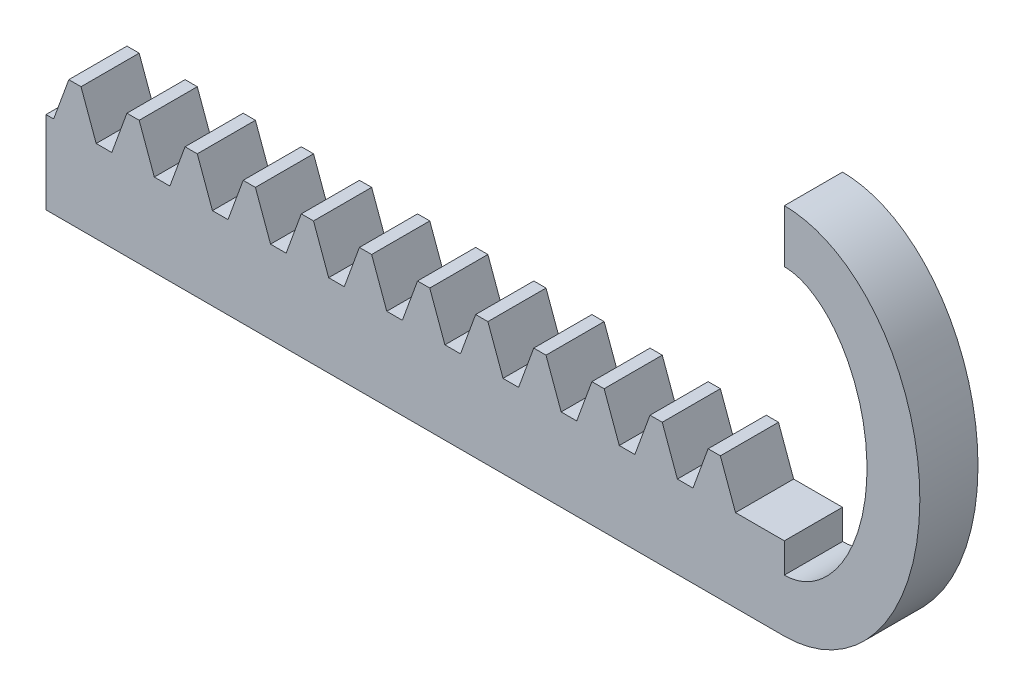
SolidWorks part; units mm, degrees
extrude "Blank" add sketch "BlankSke" against normal blind 10
sketch "BlankSke" plane through (0, 0, 0) normal (0, 0, 1) x (1, 0, 0)
  line L1 (0, 0) -> (100, 0)
  line L2 (0, 0) -> (0, 11.75)
  line L3 (0, 11.75) -> (100, 11.75)
  line L4 (100, 0) -> (100, 11.75)
  dimension "Length" = 100
  dimension "Blank_height" = 11.75
ref_plane "Plane1" through (0, 0, 0) normal (0, 0, 1) x (1, 0, 0)
ref_plane "Plane2" through (0, 0, 0) normal (0, 1, 0) x (1, 0, 0)
ref_plane "Plane3" through (0, 0, 0) normal (1, 0, 0) x (0, 0, -1)
other "Configuration Table"
sketch "HoldingSke" plane through (0, 0, 0) normal (0, 1, 0) x (1, 0, 0)
  line L0 (0, 0) -> (0.0795, 0.5659)
  line L1 (-15, 0) -> (100, 0) construction
  line L2 (0, 0) -> (-2.1039, 2.3779)
  line L3 (0, 0) -> (-11.863, 4.5341)
  line L4 (0, 0) -> (8.1152, 2.9537)
  line L5 (0, 0) -> (-23.7986, -8.8762)
  line L6 (0, 0) -> (-10.5278, -7.1032)
  line L9 (-71.009, 38.7566) -> (22.9603, 72.9586)
  line L10 (-76.2, 4.1279) -> (-66.2, 4.1279)
  line L11 (0, 0) -> (-10, 0)
  line L12 (-76.2, 101.6) -> (-76.147, 101.6)
  line L13 (24.9733, 27.94) -> (52.9518, 28.4284)
  line L14 (24.9733, 27.94) -> (24.9743, 27.94)
  line L15 (24.9733, 27.94) -> (100.4006, 29.5858)
  circle A0 centre (0, 0) radius 19.05
  circle A1 centre (0, 0) radius 5
  circle A2 centre (0, 0) radius 12.7
  dimension "MPH" = 10
  dimension "Diameter" = 38.1
  dimension "Num_teeth" = 20
  dimension "Pitch" = 0.5714
  dimension "Show_teeth" = 998
  dimension "Thickness" = 12.7
  dimension "Ap" = 20
  dimension "Pitch_height" = 10
  dimension "Width" = 10
  dimension "Backlash" = 0.053
  dimension "Addendum_fac" = 1
  dimension "Dedendum_fac" = 1.25
  dimension "Clearance_fac" = 0.25
  dimension "Dedendum_add" = 0.001
  dimension "Length" = 100
  dimension "Module" = 1.75
sketch "TooCutSkeIll" plane through (0, 0, 0) normal (0, 0, 1) x (1, 0, 0)
  line L0 (-2.1536, 11.7039) -> (-0.8423, 8.101)
  line L1 (-0.4302, 7.8125) -> (0.4302, 7.8125)
  line L2 (0.8423, 8.101) -> (2.1536, 11.7039)
  line L3 (100, 11.75) -> (0, 11.75) construction
  line L4 (0, 0) -> (0, 64.897) construction
  line L5 (-13.208, 10) -> (12.954, 10) construction
  line L6 (0, 0) -> (100, 0) construction
  line L7 (1.5334, 10) -> (1.5334, 48.7463) construction
  line L8 (-1.5334, 10) -> (-1.5334, 48.7463) construction
  line L9 (2.2194, 11.75) -> (2.2194, 11.7754)
  line L10 (-2.2194, 11.75) -> (-2.2194, 11.7754)
  line L11 (-2.2194, 11.7754) -> (2.2194, 11.7754)
  arc A0 (0.4302, 7.8125) -> (0.8423, 8.101) centre (0.4302, 8.251) ccw
  arc A1 (-0.8423, 8.101) -> (-0.4302, 7.8125) centre (-0.4302, 8.251) ccw
  arc A2 (2.2194, 11.75) -> (2.1536, 11.7039) centre (2.2194, 11.68) ccw
  arc A3 (-2.1536, 11.7039) -> (-2.2194, 11.75) centre (-2.2194, 11.68) ccw
  dimension "Pitch_height" = 10
  dimension "Addendum_plus" = 1.7754
  dimension "Pressure_angle" = 20
  dimension "Gap_width" = 3.0669
  dimension "Dedendum" = 2.1875
extrude "ToothCutIll" [suppressed] cut sketch "TooCutSkeIll" against normal through all
sketch "TooCutSkeSim" plane through (0, 0, 0) normal (0, 0, 1) x (1, 0, 0)
  line L0 (0.7373, 7.8125) -> (-0.7373, 7.8125)
  line L1 (2.1796, 11.7754) -> (0.7373, 7.8125)
  line L2 (0, 17.4625) -> (0, 53.467) construction
  line L3 (2.1796, 11.7754) -> (-2.1796, 11.7754)
  line L6 (-2.1796, 11.7754) -> (-0.7373, 7.8125)
  line L9 (-1.5334, 10) -> (1.5334, 10) construction
  line L10 (0, 0) -> (100, 0) construction
  line L11 (1.5334, 10) -> (1.5334, 53.467) construction
  line L12 (-1.5334, 10) -> (-1.5334, 53.467) construction
  dimension "Pitch_height" = 10
  dimension "Addendum_plus" = 1.7754
  dimension "Pressure_angle" = 20
  dimension "Gap_width" = 3.0669
  dimension "Dedendum" = 2.1875
extrude "ToothCutSim" cut sketch "TooCutSkeSim" against normal through all
pattern_linear "TeethCuts" count 19 spacing 5.4978 along (1, 0, 0) of "ToothCutIll", "ToothCutSim"
sketch "草图3" plane through (0, 0, 0) normal (0, 0, 1) x (1, 0, 0)
  line L0 (100, 0) -> (102.8415, 0)
  line L1 (102.8415, 0) -> (102.8415, 7.8125)
  line L2 (102.8415, 7.8125) -> (100, 7.8125)
  line L3 (100, 7.8125) -> (100, 0)
  line L4 (100, 0) -> (100, 8.6438) construction
  line L5 (98.2229, 7.8125) -> (99.6974, 7.8125) construction
extrude "凸台-拉伸1" add sketch "草图3" against normal up to surface (10 mm away) contours L3 L0 L1 L2 up to face at (50.1593, 9.4613, -10)
sketch "草图5" plane through (0, 0, 0) normal (0, 0, 1) x (1, 0, 0)
  line L0 (102.8415, 0.3026) -> (102.8415, 8.9464) construction
  line L1 (102.8415, 0) -> (102.8415, 5)
  line L2 (102.8415, 35.2664) -> (102.8415, 30.2664)
  arc A0 (102.8415, 0) -> (102.8415, 35.2664) centre (102.8415, 17.6332) ccw construction
  ellipse E0 centre (102.8415, 17.6332) end of major axis (102.8415, 35.2664) minor radius 12.82 (102.8415, 0) -> (102.8415, 35.2664) ccw
  spline S0 degree 1 poles (102.8415, 5) (102.8415, 30.2664) knots 0 0 1 1 construction
  spline S1 degree 3 poles (102.8415, 5) (103.239, 5) (104.0058, 5.1028) (105.6778, 5.7786) (107.9569, 7.7782) (110.1255, 12.1377) (110.9296, 17.6332) (110.1255, 23.1287) (107.9569, 27.4882) (105.6778, 29.4878) (104.0058, 30.1636) (103.239, 30.2664) (102.8415, 30.2664) knots 3.141593 3.141593 3.141593 3.141593 3.337942 3.534292 3.926991 4.31969 4.712389 5.105088 5.497787 5.890486 6.086836 6.283185 6.283185 6.283185 6.283185
  dimension "D1" = 5
extrude "凸台-拉伸2" add sketch "草图5" against normal blind 5.5 contours L2 S1 L1 E0
sketch "草图6" plane through (0, 0, -10) normal (0, 0, -1) x (-1, 0, 0)
  line L1 (-102.8415, 0) -> (0, 0)
  line L2 (-102.8415, 0) -> (-102.8415, 15)
  line L3 (-102.8415, 15) -> (0, 15)
  line L4 (0, 0) -> (0, 15)
  dimension "D1" = 15
extrude "切除-拉伸2" cut sketch "草图6" against normal blind 4.5 contours L2 L1 L4 L3
sketch "草图7" plane through (0, 0, 0) normal (0, 0, 1) x (1, 0, 0)
  line L0 (102.8415, 7.8125) -> (100, 7.8125) construction
  line L1 (99.3518, 9.0173) -> (100.512, 9.0173)
  line L2 (99.3518, 9.0173) -> (99.3518, 7.8125)
  line L3 (99.3518, 7.8125) -> (100.512, 7.8125)
  line L4 (100.512, 9.0173) -> (100.512, 7.8125)
extrude "切除-拉伸3" cut sketch "草图7" against normal up to surface (5.5 mm away) up to face at (53.9987, 9.566, -5.5)
sketch "草图8" plane through (0, 0, 0) normal (-1, 0, 0) x (0, 0, 1)
  line L1 (8.3331, -13.325) -> (-8.3331, -13.325)
  line L2 (8.3331, -13.325) -> (8.3331, 13.325)
  line L3 (8.3331, 13.325) -> (-8.3331, 13.325)
  line L4 (-8.3331, -13.325) -> (-8.3331, 13.325)
  line L5 (8.3331, -13.325) -> (-8.3331, 13.325) construction
  line L6 (8.3331, 13.325) -> (-8.3331, -13.325) construction
  point P0 (0, 0)
extrude "切除-拉伸5" cut sketch "草图8" against normal blind 33
sketch "草图9" plane through (0, 0, 0) normal (0, 0, 1) x (1, 0, 0)
  ellipse E0 centre (102.8415, 17.6332) end of major axis (102.8415, 35.2664) minor radius 12.82 (102.8415, 0) -> (102.8415, 35.2664) ccw construction
  point P0 (115.6438, 16.7056)
sketch "草图10" plane through (0, 0, 0) normal (0, 0, 1) x (1, 0, 0)
  ellipse E0 centre (102.8415, 17.6332) end of major axis (102.8415, 35.2664) minor radius 12.82 (102.8415, 0) -> (102.8415, 35.2664) ccw construction
  point P0 (115.6328, 16.454)
equation "' \"Module@HoldingSke\" = 6.35"
equation "' \"Num_teeth@HoldingSke\" = 12"
equation "' \"Ap@HoldingSke\" =  20"
equation "' \"Ap@HoldingSke\" = 20"
equation "' \"Width@HoldingSke\" = 0.25 * 25.4"
equation "' \"Show_teeth@HoldingSke\" = 500"
equation "' \"Backlash@HoldingSke\" = 0.009 * 25.4"
equation "' \"Addendum_fac@HoldingSke\" = 1.0"
equation "' \"Dedendum_fac@HoldingSke\" = 1.25"
equation "' \"Dedendum_add@HoldingSke\" = 0.00005 * 25.4"
equation "' \"Clearance_fac@HoldingSke\" = 0.25"
equation "' \"Pitch_height@HoldingSke\" = 1 * 25.4"
equation "' \"Length@HoldingSke\" = 4.71 * 25.4"
equation "\"Pitch@HoldingSke\" = 1 / \"Module@HoldingSke\""
equation "\"MPH@HoldingSke\" = \"Dedendum_fac@HoldingSke\" / \"Pitch@HoldingSke\" + 2 * \"Dedendum_add@HoldingSke\" + 0.002 * 25.4"
equation "\"MPH@HoldingSke\" = ((sgn( \"MPH@HoldingSke\" - \"Pitch_height@HoldingSke\")+1)*( \"MPH@HoldingSke\" - \"Pitch_height@HoldingSke\"))/2 + \"Pitch_height@HoldingSke\""
equation "\"Blank_height@BlankSke\" = \"Pitch_height@HoldingSke\" + \"Addendum_fac@HoldingSke\"  / \"Pitch@HoldingSke\" "
equation "\"Length@BlankSke\" =  \"Length@HoldingSke\""
equation "\"Face_width@Blank\" = \"Width@HoldingSke\""
equation "\"Pressure_angle@TooCutSkeIll\" = \"Ap@HoldingSke\""
equation "\"Addendum_plus@TooCutSkeIll\" =  \"Addendum_fac@HoldingSke\"  / \"Pitch@HoldingSke\" + 0.001 *25.4"
equation "\"Dedendum@TooCutSkeIll\" = \"Dedendum_fac@HoldingSke\"  / \"Pitch@HoldingSke\""
equation "\"Pitch_height@TooCutSkeIll\" =  \"MPH@HoldingSke\""
equation "\"Gap_width@TooCutSkeIll\" = 3.14159265 / 2 / \"Pitch@HoldingSke\" + 6 * \"Backlash@HoldingSke\""
equation "\"Pressure_angle@TooCutSkeSim\" = \"Ap@HoldingSke\""
equation "\"Addendum_plus@TooCutSkeSim\" =  \"Addendum_fac@HoldingSke\"  / \"Pitch@HoldingSke\" + 0.001 * 25.4"
equation "\"Dedendum@TooCutSkeSim\" = \"Dedendum_fac@HoldingSke\"  / \"Pitch@HoldingSke\""
equation "\"Pitch_height@TooCutSkeSim\" =  \"MPH@HoldingSke\""
equation "\"Gap_width@TooCutSkeSim\" = 3.14159265 / 2 / \"Pitch@HoldingSke\" + 6 * \"Backlash@HoldingSke\""
equation "\"Root_fillet@TooCutSkeIll\" = \"Clearance_fac@HoldingSke\" / \"Pitch@HoldingSke\" + \"Dedendum_add@HoldingSke\""
equation "\"Break_rad@TooCutSkeIll\" = 0.02 / \"Pitch@HoldingSke\" * 2"
equation "\"Linear_pitch@TeethCuts\" = 3.14159265 / \"Pitch@HoldingSke\""
equation "\"Num_teeth@HoldingSke\" = int( ( \"Length@HoldingSke\" + 0 ) / (3.14159265 / \"Pitch@HoldingSke\")) + 0.9999  + 1"
equation " \"Num_teeth@TeethCuts\" = int( \"Show_teeth@HoldingSke\" ) + 1"
equation " \"Num_teeth@TeethCuts\" = ((sgn( \"Num_teeth@TeethCuts\" - \"Num_teeth@HoldingSke\" )-1)*( \"Num_teeth@TeethCuts\" - \"Num_teeth@HoldingSke\" ))/-2+ \"Num_teeth@HoldingSke\""
equation " \"Num_teeth@TeethCuts\" = ((sgn( \"Num_teeth@TeethCuts\" - 2.0)+1)*( \"Num_teeth@TeethCuts\" - 2.0))/2 +2.0"
